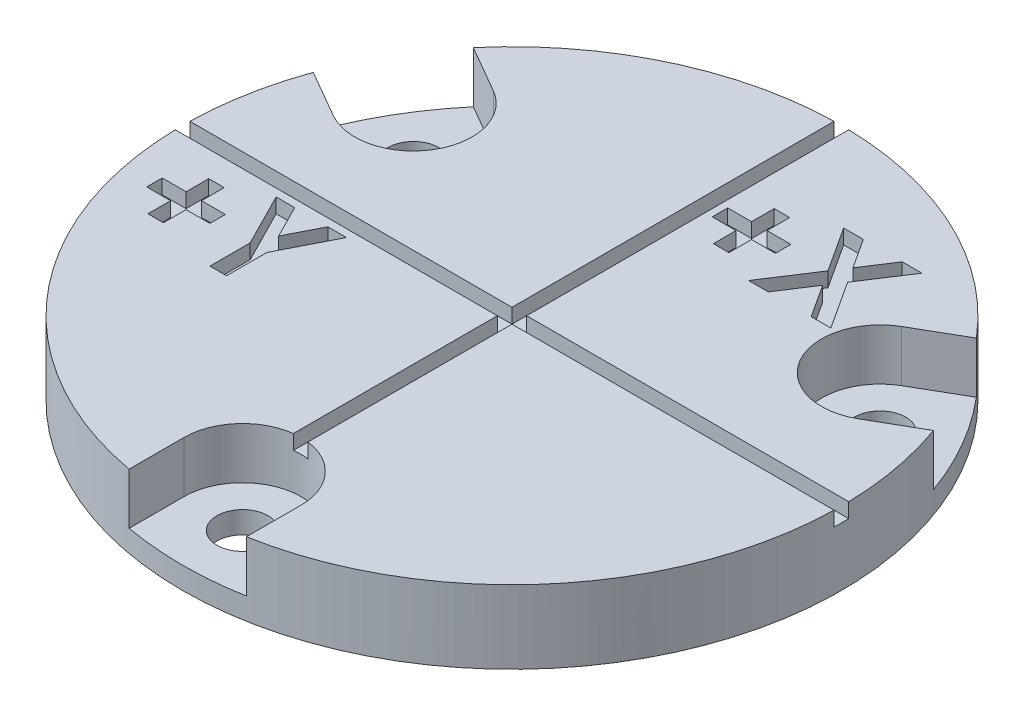
SolidWorks part; units mm, degrees
ref_plane "Front" through (0, 0, 0) normal (0, 0, 1) x (1, 0, 0)
ref_plane "Top" through (0, 0, 0) normal (0, 1, 0) x (1, 0, 0)
ref_plane "Right" through (0, 0, 0) normal (1, 0, 0) x (0, 0, -1)
sketch "Sketch1" plane through (0, 0, 0) normal (0, 1, 0) x (1, 0, 0)
  line L0 (0, 22.5) -> (0, -22.5) construction
  line L1 (22.5, 0) -> (-22.5, 0) construction
  circle A0 centre (0, 0) radius 22.5
  circle A1 centre (0, 0) radius 18.4 construction
  arc A2 (-10.9795, -19.6393) -> (-7.9114, -21.0632) centre (-9.4455, -20.3512) cw construction
  point P19 (0, 0)
  dimension "D1" = 45
  dimension "D2" = 36.8
extrude "plate" add sketch "Sketch1" along normal blind 5
sketch "Sketch6" plane through (0, 5, 0) normal (0, 1, 0) x (1, 0, 0)
  line L0 (0, 22.5) -> (0, -22.5) construction
  line L1 (0, -22.5) -> (0, -18.4) construction
  line L2 (-4, -22.5) -> (-4, -18.4)
  line L3 (4, -22.5) -> (4, -18.4)
  circle A1 centre (0, 0) radius 18.4 construction
  circle A2 centre (0, 0) radius 22.5 construction
  arc A3 (-4, -22.5) -> (4, -22.5) centre (0, -22.5) ccw
  arc A4 (4, -18.4) -> (-4, -18.4) centre (0, -18.4) ccw
  point P7 (0, -20.45)
  dimension "D1" = 4
extrude "opening for screw" cut sketch "Sketch6" against normal blind 5 from offset 1.5 contours L3 A4 L2 A3
sketch "Sketch7" plane through (0, 1.5, 0) normal (0, 1, 0) x (1, 0, 0)
  line L0 (0, 22.5) -> (0, -22.5) construction
  circle A0 centre (0, -18.4) radius 1.75
  circle A1 centre (0, 0) radius 18.4 construction
  point P2 (0, 0)
  dimension "D1" = 3.5
extrude "screw hole" cut sketch "Sketch7" against normal blind 5
pattern_circular "CirPattern20" count 3 over 360 about axis through (0, 0, 0) along (0, 1, 0) of "opening for screw", "screw hole"
sketch "Sketch10" plane through (0, 5, 0) normal (0, 1, 0) x (1, 0, 0)
  line L1 (-22.5, 0.5) -> (22.5, 0.5)
  line L2 (-22.5, 0.5) -> (-22.5, -0.5)
  line L3 (-22.5, -0.5) -> (22.5, -0.5)
  line L4 (22.5, 0.5) -> (22.5, -0.5)
  line L5 (-0.5, 22.5) -> (0.5, 22.5)
  line L6 (-0.5, 22.5) -> (-0.5, -22.5)
  line L7 (-0.5, -22.5) -> (0.5, -22.5)
  line L8 (0.5, 22.5) -> (0.5, -22.5)
  line L9 (0, 22.5) -> (0, -22.5) construction
  point P4 (22.5, 0)
  point P9 (-22.5, 0)
  point P14 (0, -22.5)
  point P15 (0, 22.5)
  point P19 (-2.0585, 12.7822)
  point P20 (-4.7401, 12.405)
  point P22 (-18.9752, -6.3427)
  point P23 (0, 0)
  point P24 (-18.8339, -7.6497)
  point P25 (1.0987, 13.1019)
  point P26 (1.3556, 11.6943)
  point P27 (0, 0)
  point P28 (0.5, 11.933)
  dimension "D1" = 1
  dimension "D2" = 1
extrude "Cut-Extrude5" cut sketch "Sketch10" against normal blind 1 contours L6 L7 L8 L5 | L1 L4 L3 L2
sketch "Sketch11" plane through (0, 5, 0) normal (0, 1, 0) x (1, 0, 0)
  line L0 (0.5, 22.4944) -> (0.5, 0.5) construction
  text T0 "<b>+X</b>"
  text T1 "<b>+Y</b>"
  point P1 (1.2612, 8.3302)
  point P2 (0, 0)
  point P3 (0, 0)
  point P4 (0.5, 10.1604)
  point P8 (0, 0)
  point P9 (-17.4006, -2.4788)
  point P10 (-19.5952, -5.1924)
  point P11 (-20.5748, -7.3769)
extrude "Cut-Extrude6" cut sketch "Sketch11" against normal blind 1
